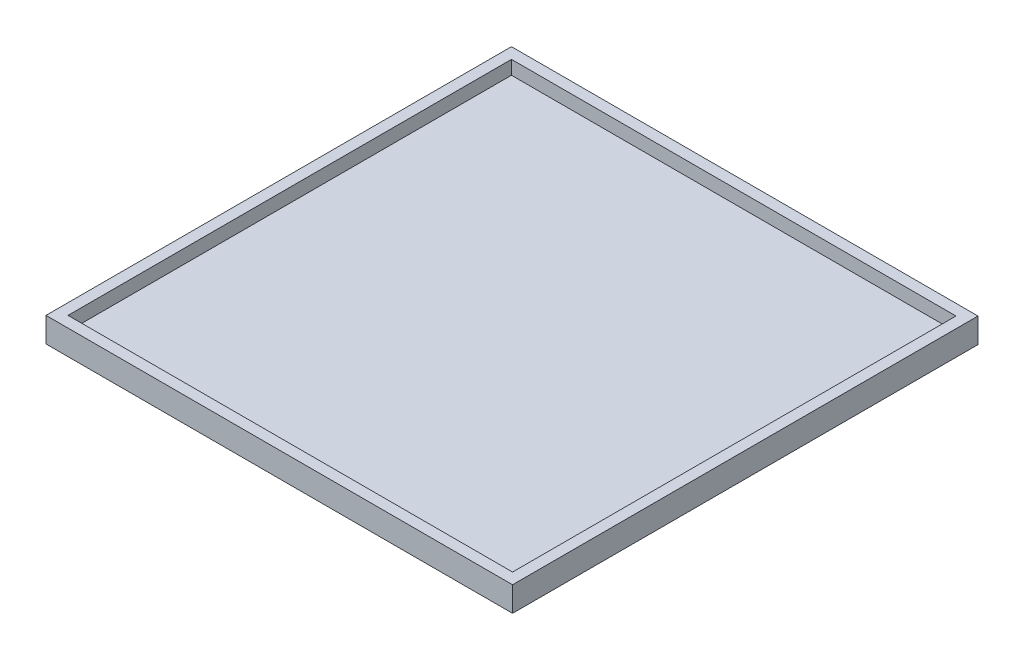
SolidWorks part; units mm, degrees
material "6061-T6 (SS)"
ref_plane "Front Plane" through (0, 0, 0) normal (0, 0, 1) x (1, 0, 0)
ref_plane "Top Plane" through (0, 0, 0) normal (0, 1, 0) x (1, 0, 0)
ref_plane "Right Plane" through (0, 0, 0) normal (1, 0, 0) x (0, 0, -1)
sketch "Sketch1" plane through (0, 0, 0) normal (0, 1, 0) x (1, 0, 0)
  line L1 (-512.7, -511.43) -> (512.7, -511.43)
  line L2 (-512.7, -511.43) -> (-512.7, 511.43)
  line L3 (-512.7, 511.43) -> (512.7, 511.43)
  line L4 (512.7, -511.43) -> (512.7, 511.43)
  line L5 (-512.7, -511.43) -> (512.7, 511.43) construction
  line L6 (-512.7, 511.43) -> (512.7, -511.43) construction
  point P0 (0, 0)
  dimension "D1" = 1025.4
  dimension "D2" = 1022.86
extrude "Boss-Extrude1" add sketch "Sketch1" along normal blind 31.75
shell "Shell1" thickness 25.4
